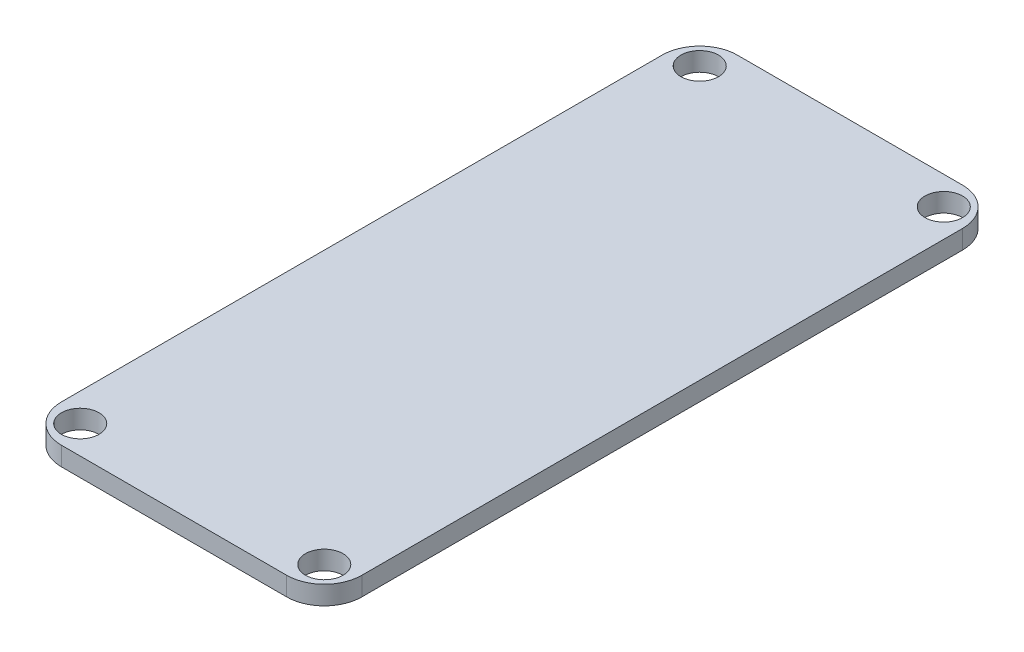
SolidWorks part; units mm, degrees
ref_plane "Front Plane" through (0, 0, 0) normal (0, 0, 1) x (1, 0, 0)
ref_plane "Top Plane" through (0, 0, 0) normal (0, 1, 0) x (1, 0, 0)
ref_plane "Right Plane" through (0, 0, 0) normal (1, 0, 0) x (0, 0, -1)
sketch "Sketch1" plane through (0, 0, 0) normal (0, 1, 0) x (1, 0, 0)
  line L1 (0, 0) -> (25.4, 0)
  line L2 (0, 0) -> (0, 57.15)
  line L3 (0, 57.15) -> (25.4, 57.15)
  line L4 (25.4, 0) -> (25.4, 57.15)
  dimension "D1" = 57.15
  dimension "D2" = 25.4
extrude "Boss-Extrude1" add sketch "Sketch1" along normal blind 1.5875
sketch "Sketch2" plane through (0, 1.5875, 0) normal (0, 1, 0) x (1, 0, 0)
  line L16 (2.3812, 2.3813) -> (23.0188, 2.3813)
  line L17 (23.0188, 2.3813) -> (23.0187, 54.7687)
  line L18 (23.0187, 54.7687) -> (2.3812, 54.7687)
  line L19 (2.3812, 54.7687) -> (2.3812, 2.3813)
  line L20 (2.3812, 2.3813) -> (23.0188, 2.3813) construction
  line L21 (23.0188, 2.3813) -> (23.0187, 54.7687) construction
  line L22 (23.0187, 54.7687) -> (2.3812, 54.7687) construction
  line L23 (2.3812, 54.7687) -> (2.3812, 2.3813) construction
  circle A0 centre (2.3812, 54.7687) radius 1.5875
  circle A1 centre (23.0187, 54.7687) radius 1.5875
  circle A2 centre (23.0188, 2.3813) radius 1.5875
  circle A3 centre (2.3812, 2.3813) radius 1.5875
  point P2 (0, 0)
  point P3 (6.4687, 50.6161)
  point P4 (2.7094, 54.7687)
  point P6 (23.0187, 54.427)
  point P8 (23.0188, 2.723)
  point P10 (2.7094, 2.3813)
  dimension "D1" = 3.175
  dimension "D2" = 2.3813
extrude "Cut-Extrude2" cut sketch "Sketch2" against normal through all
fillet "Fillet1" radius 3.175 4 edges at (0, 0.7937, -57.15) (25.4, 0.7937, -57.15) (25.4, 0.7937, 0) (0, 0.7937, 0)
